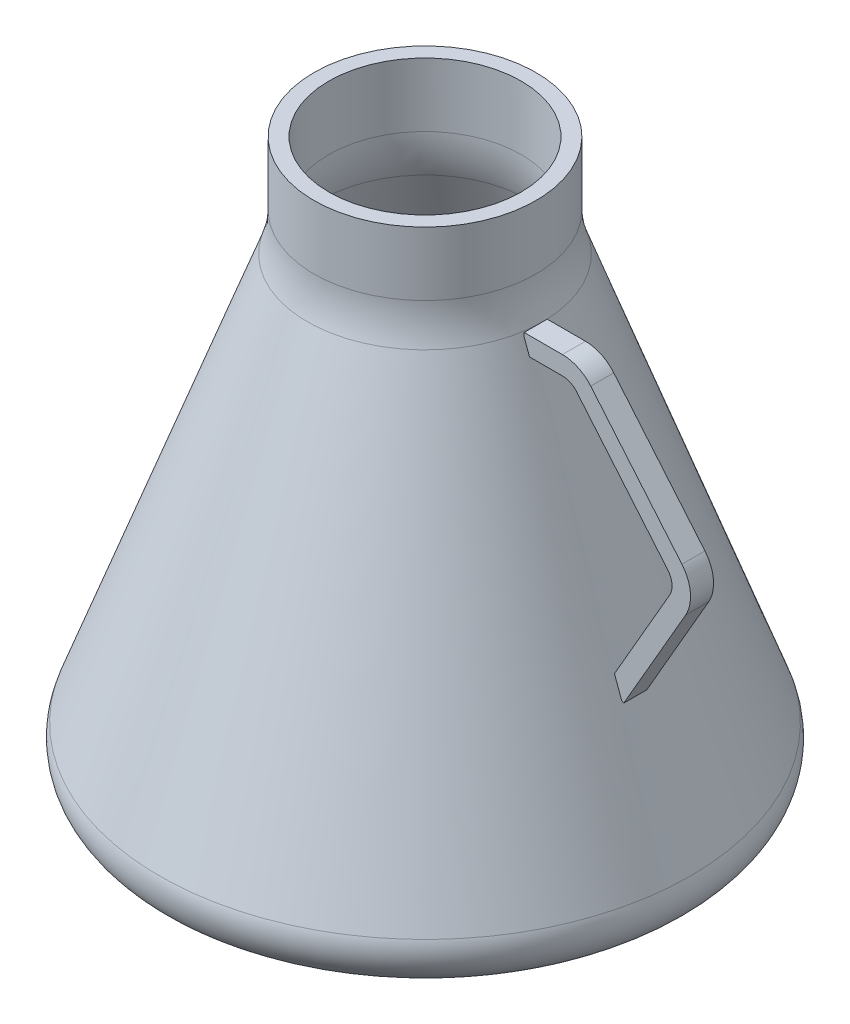
SolidWorks part; units mm, degrees
ref_plane "Front Plane" through (0, 0, 0) normal (0, 0, 1) x (1, 0, 0)
ref_plane "Top Plane" through (0, 0, 0) normal (0, 1, 0) x (1, 0, 0)
ref_plane "Right Plane" through (0, 0, 0) normal (1, 0, 0) x (0, 0, -1)
sketch "Sketch2" plane through (0, 0, 0) normal (0, 0, 1) x (1, 0, 0)
  line L0 (-8.8745, 12.6394) -> (-8.8745, -21.7809)
  line L1 (-8.8745, 12.6394) -> (51.1255, 12.6394)
  line L2 (-12.4929, -42.3021) -> (-102.1764, -288.7055)
  line L3 (51.1255, 12.6394) -> (51.1255, -288.7055)
  line L4 (51.1255, -288.7055) -> (-102.1764, -288.7055)
  arc A0 (-8.8745, -21.7809) -> (-12.4929, -42.3021) centre (-68.8745, -21.7809) cw
  point P7 (-8.8745, -32.3606)
  dimension "D4" = 60
  dimension "D1" = 45
  dimension "D2" = 60
  dimension "D3" = 20
revolve "Revolve2" add sketch "Sketch2" angle 360 about L3
shell "Shell1" thickness 8
fillet "Fillet1" radius 12 1 edges at (-90.7512, -280.7055, 0)
fillet "Fillet3" radius 20 1 edges at (-102.1764, -288.7055, 0)
sketch "Sketch3" plane through (0, 0, 0) normal (0, 0, 1) x (1, 0, 0)
  line L0 (114.7439, -42.3021) -> (135.4178, -42.3021)
  line L1 (150.7387, -49.4464) -> (200.021, -108.1788)
  line L2 (202.0206, -131.0345) -> (168.6082, -188.9066)
  arc A0 (200.021, -108.1788) -> (202.0206, -131.0345) centre (184.7001, -121.0345) cw
  arc A1 (135.4178, -42.3021) -> (150.7387, -49.4464) centre (135.4178, -62.3021) cw
  point P8 (209.0227, -118.9066)
  point P11 (144.7439, -42.3021)
  dimension "D5" = 20
  dimension "D6" = 20
  dimension "D1" = 130
  dimension "D2" = 100
  dimension "D3" = 110
  dimension "D4" = 70
extrude "Extrude-Thin1" add sketch "Sketch3" along normal blind 10 and the other way blind 2.4518 thin
